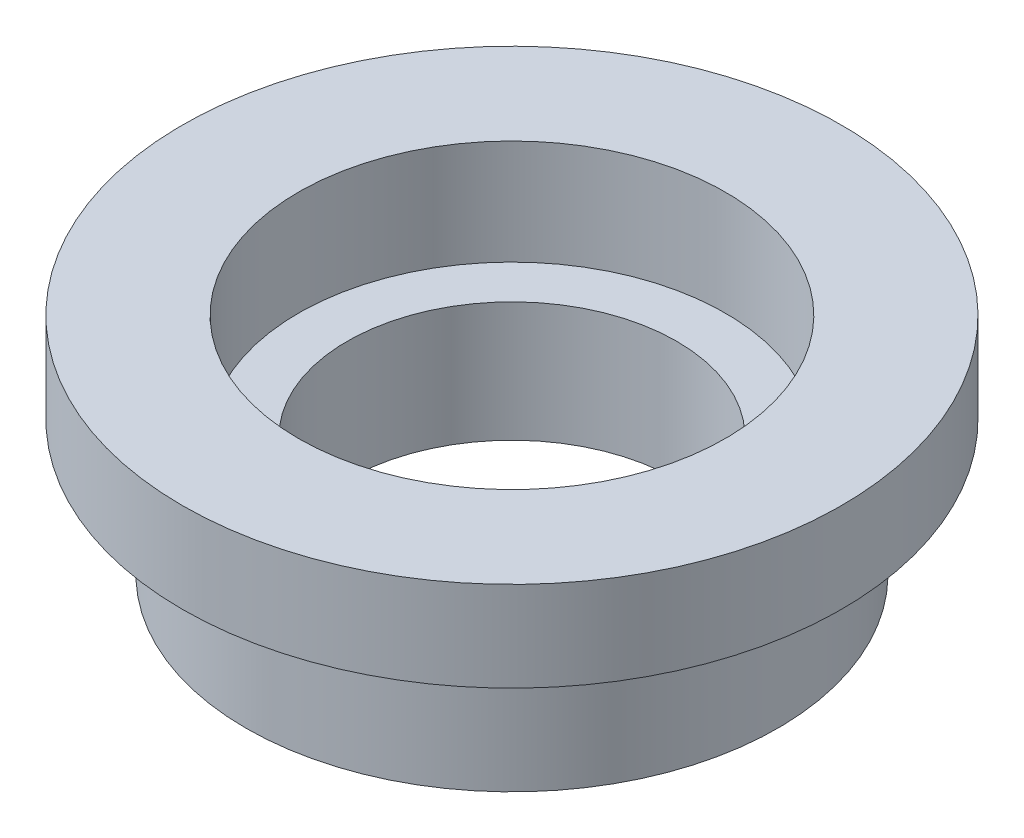
SolidWorks part; units mm, degrees
ref_plane "Front Plane" through (0, 0, 0) normal (0, 0, 1) x (1, 0, 0)
ref_plane "Top Plane" through (0, 0, 0) normal (0, 1, 0) x (1, 0, 0)
ref_plane "Right Plane" through (0, 0, 0) normal (1, 0, 0) x (0, 0, -1)
sketch "Sketch1" plane through (0, 0, 0) normal (0, 1, 0) x (1, 0, 0)
  circle A0 centre (0, 0) radius 7.125 construction
  circle A1 centre (0, 0) radius 8.875
  circle A2 centre (0, 0) radius 5.5
  dimension "D1" = 14.25
  dimension "D2" = 17.75
  dimension "D3" = 11
extrude "Boss-Extrude1" add sketch "Sketch1" along normal mid plane 4
sketch "Sketch2" plane through (0, 2, 0) normal (0, 1, 0) x (1, 0, 0)
  circle A0 centre (0, 0) radius 7.125
  circle A1 centre (0, 0) radius 9
  dimension "D1" = 14.25
extrude "Boss-Extrude2" add sketch "Sketch2" along normal blind 3.5
sketch "Sketch3" plane through (0, 5.5, 0) normal (0, 1, 0) x (1, 0, 0)
  circle A0 centre (0, 0) radius 9
  circle A1 centre (0, 0) radius 11
  dimension "D1" = 22
extrude "Boss-Extrude3" add sketch "Sketch3" against normal blind 3
